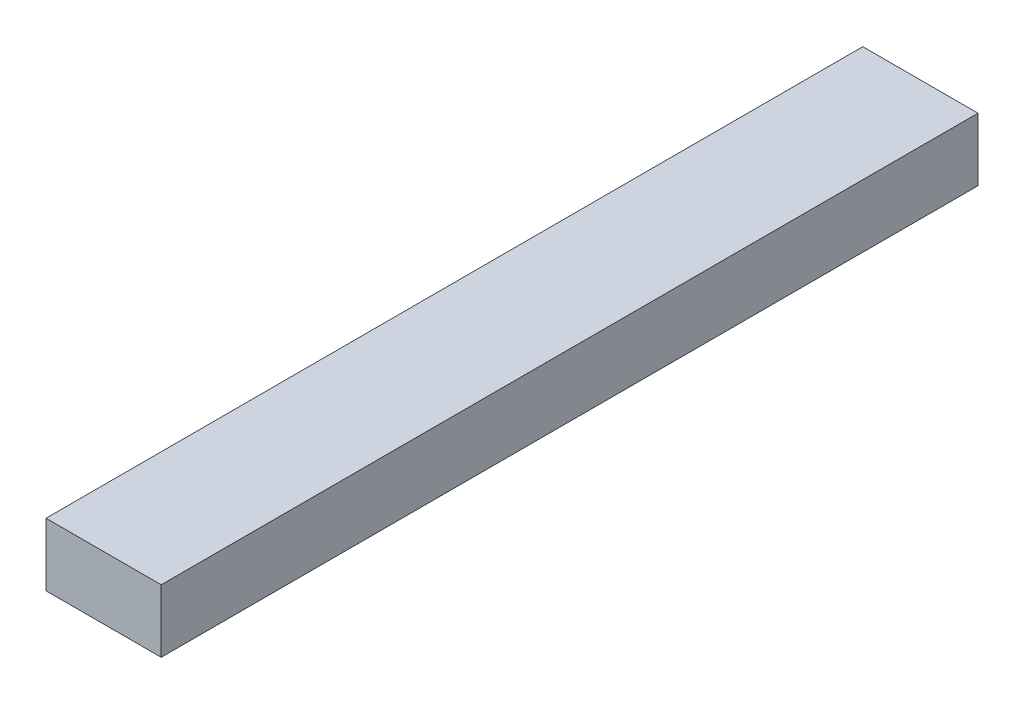
SolidWorks part; units mm, degrees
material "Простая углеродистая сталь"
ref_plane "Спереди" through (0, 0, 0) normal (0, 0, 1) x (1, 0, 0)
ref_plane "Сверху" through (0, 0, 0) normal (0, 1, 0) x (1, 0, 0)
ref_plane "Справа" through (0, 0, 0) normal (1, 0, 0) x (0, 0, -1)
sketch "Эскиз1" plane through (0, 0, 0) normal (0, 1, 0) x (1, 0, 0)
  line L1 (0, 0) -> (55, 0)
  line L2 (0, 0) -> (0, 390)
  line L3 (0, 390) -> (55, 390)
  line L4 (55, 0) -> (55, 390)
extrude "Бобышка-Вытянуть1" add sketch "Эскиз1" along normal blind 30
